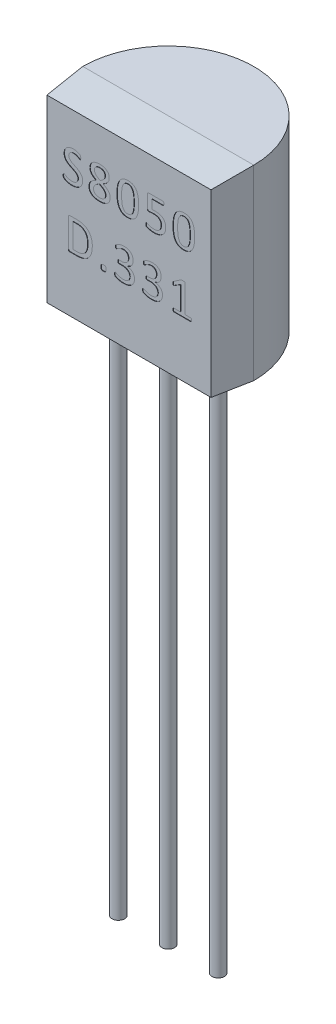
SolidWorks part; units mm, degrees
material "6061-T6 (SS)"
ref_plane "Front Plane" through (0, 0, 0) normal (0, 0, 1) x (1, 0, 0)
ref_plane "Top Plane" through (0, 0, 0) normal (0, 1, 0) x (1, 0, 0)
ref_plane "Right Plane" through (0, 0, 0) normal (1, 0, 0) x (0, 0, -1)
sketch "Sketch1" plane through (0, 0, 0) normal (0, 1, 0) x (1, 0, 0)
  line L0 (-2.175, 0) -> (2.175, 0)
  line L4 (0, 0) -> (0, -1.075) construction
  line L5 (0, 0) -> (0, 2.175) construction
  arc A0 (2.175, 0) -> (-2.175, 0) centre (0, 0) ccw
  dimension "D1" = 4.35
extrude "Boss-Extrude1" add sketch "Sketch1" along normal blind 4.75
sketch "Sketch2" plane through (0, 0, 0) normal (0, 0, 1) x (1, 0, 0)
  line L4 (-2.175, 0) -> (2.175, 0)
  line L5 (2.175, 0) -> (2.175, 4.75)
  line L6 (2.175, 4.75) -> (-2.175, 4.75)
  line L7 (-2.175, 4.75) -> (-2.175, 0)
  line L8 (-2.175, 0) -> (2.175, 0)
  line L9 (2.175, 0) -> (2.175, 4.75)
  line L10 (2.175, 4.75) -> (-2.175, 4.75)
  line L11 (-2.175, 4.75) -> (-2.175, 0)
  dimension "D1" = 0
extrude "Boss-Extrude2" add sketch "Sketch2" along normal blind 1 draft 5
sketch "Sketch3" plane through (0, 0, 1) normal (0, 0, 1) x (1, 0, 0)
  line L0 (0, 0) -> (0, 1.5) construction
  line L1 (0, 1.5) -> (0, 3) construction
  line L2 (-2.0875, 1.5) -> (2.0875, 1.5) construction
  line L3 (-2.0875, 4.6625) -> (-2.0875, 0.0875) construction
  line L4 (-2.0875, 3) -> (2.0875, 3) construction
  text T0 "S8050" font "Calibri" height 0.8
  text T1 "D.331" font "Calibri" height 0.8
  point P6 (-2.0875, 2.9145)
  dimension "D1" = 1.5
  dimension "D2" = 3
extrude "Cut-Extrude1" cut sketch "Sketch3" against normal blind 0.01
sketch "Sketch4" plane through (0, 0, 0) normal (0, -1, 0) x (1, 0, 0)
  line L0 (-1.27, 0) -> (1.27, 0) construction
  circle A0 centre (0, 0) radius 0.16
  circle A1 centre (1.27, 0) radius 0.16
  circle A2 centre (-1.27, 0) radius 0.16
  dimension "D2" = 0.32
  dimension "D1" = 2.54
extrude "Boss-Extrude3" add sketch "Sketch4" along normal blind 13.5 and the other way blind 1 separate body
